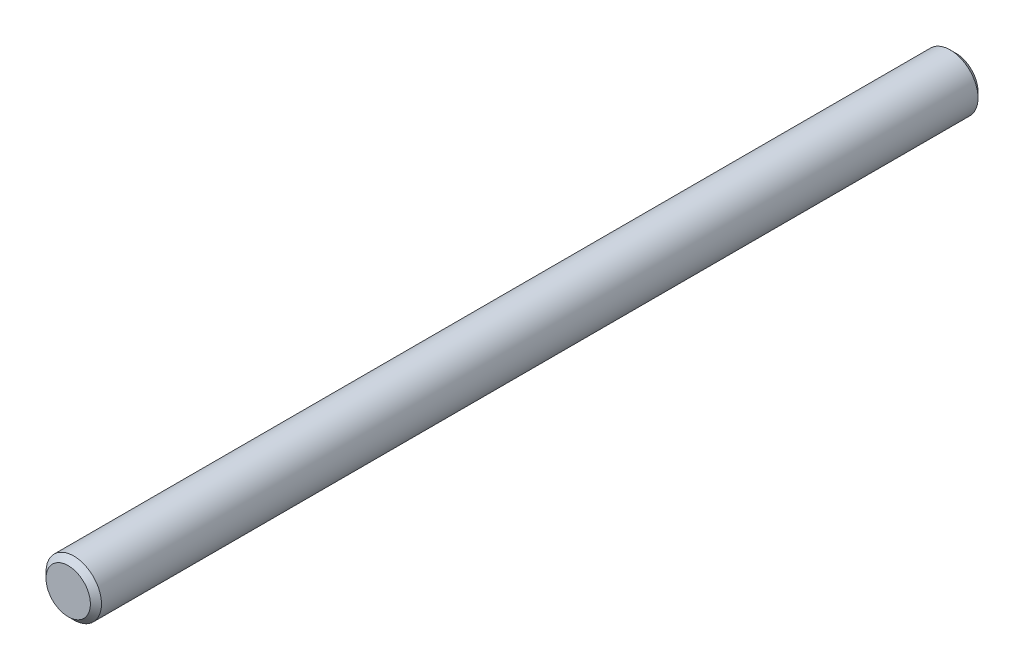
SolidWorks part; units mm, degrees
material "Plain Carbon Steel"
ref_plane "Front" through (0, 0, 0) normal (0, 0, 1) x (1, 0, 0)
ref_plane "Top" through (0, 0, 0) normal (0, 1, 0) x (1, 0, 0)
ref_plane "Right" through (0, 0, 0) normal (1, 0, 0) x (0, 0, -1)
sketch "Sketch1" plane through (0, 0, 0) normal (0, 0, 1) x (1, 0, 0)
  circle A0 centre (0, 0) radius 9.525
  dimension "dia" = 19.05
extrude "Extrude1" add sketch "Sketch1" along normal mid plane 304.8
sketch "Sketch2" plane through (0, 0, 0) normal (1, 0, 0) x (0, 0, -1)
  line L0 (152.4, 9.525) -> (149.86, 9.525) construction
  line L1 (152.4, 9.525) -> (-152.4, 9.525) construction
  line L2 (149.86, 9.525) -> (118.9037, 9.525) construction
  line L3 (118.9037, 9.525) -> (111.76, 9.525) construction
  line L4 (111.76, 9.525) -> (109.22, 9.525) construction
  line L5 (109.22, 9.525) -> (106.5632, 9.525) construction
  line L7 (97.6732, 9.525) -> (92.9107, 9.525) construction
  line L8 (92.9107, 9.525) -> (81.4807, 9.525) construction
  line L10 (-152.4, -9.525) -> (152.4, -9.525) construction
  line L11 (-152.4, 9.525) -> (-149.86, 9.525) construction
  line L12 (-149.86, 9.525) -> (-149.86, -9.525) construction
  line L13 (106.5632, 9.525) -> (97.6732, 9.525) construction
  line L14 (97.6732, 9.525) -> (97.6732, -9.525) construction
  line L15 (111.76, 9.525) -> (111.76, -9.525) construction
  line L16 (81.4807, 9.525) -> (76.7182, 9.525) construction
  line L17 (76.7182, 9.525) -> (65.2882, 9.525) construction
  line L18 (65.2882, 9.525) -> (60.5257, 9.525) construction
  line L19 (60.5257, 9.525) -> (49.0957, 9.525) construction
  line L20 (81.4807, 9.525) -> (81.4807, -9.525) construction
  line L21 (65.2882, 9.525) -> (65.2882, -9.525) construction
  line L22 (49.0957, 9.525) -> (49.0957, -9.525) construction
  line L23 (49.0957, 9.525) -> (44.3332, 9.525) construction
  line L24 (44.3332, 9.525) -> (32.9032, 9.525) construction
  line L25 (32.9032, 9.525) -> (32.9032, -9.525) construction
  line L26 (32.9032, 9.525) -> (28.1407, 9.525) construction
  line L27 (28.1407, 9.525) -> (16.7107, 9.525) construction
  line L28 (16.7107, 9.525) -> (11.9482, 9.525) construction
  line L29 (11.9482, 9.525) -> (0.5182, 9.525) construction
  line L30 (16.7107, 9.525) -> (16.7107, -9.525) construction
  line L31 (0.5182, 9.525) -> (0.5182, -9.525) construction
  line L32 (0.5182, 9.525) -> (-4.2443, 9.525) construction
  line L33 (-4.2443, 9.525) -> (-13.1343, 9.525) construction
  line L34 (-13.1343, 9.525) -> (-15.7912, 9.525) construction
  line L35 (-15.7912, 9.525) -> (-18.3312, 9.525) construction
  line L36 (-18.3312, 9.525) -> (-18.3312, -9.525) construction
  line L37 (-18.3312, 9.525) -> (-107.2312, 9.525) construction
  line L38 (-107.2312, 9.525) -> (-107.2312, -9.525) construction
  line L39 (109.22, 9.525) -> (109.22, -9.525) construction
  point P0 (-152.4, 9.525)
  point P1 (152.4, 9.525)
  dimension "D1" = 2.54
  dimension "D2" = 30.9562
  dimension "D3" = 7.1437
  dimension "D4" = 2.54
  dimension "D5" = 2.6568
  dimension "D6" = 8.89
  dimension "D7" = 11.43
  dimension "D8" = 2.54
  dimension "D9" = 4.7625
  dimension "D10" = 4.7625
  dimension "D11" = 11.43
  dimension "D12" = 4.7625
  dimension "D13" = 11.43
  dimension "D14" = 4.7625
  dimension "D15" = 11.43
  dimension "D16" = 4.7625
  dimension "D17" = 11.43
  dimension "D18" = 4.7625
  dimension "D19" = 11.43
  dimension "D20" = 4.7625
  dimension "D21" = 8.89
  dimension "D22" = 2.6568
  dimension "D23" = 2.54
  dimension "D24" = 88.9
chamfer "Chamfer1" distance 1.905 angle 45 2 edges at (9.525, 0, -152.4) (9.525, 0, 152.4)
equation "\"D1@Chamfer1\" = \"dia@Sketch1\" * .1"
